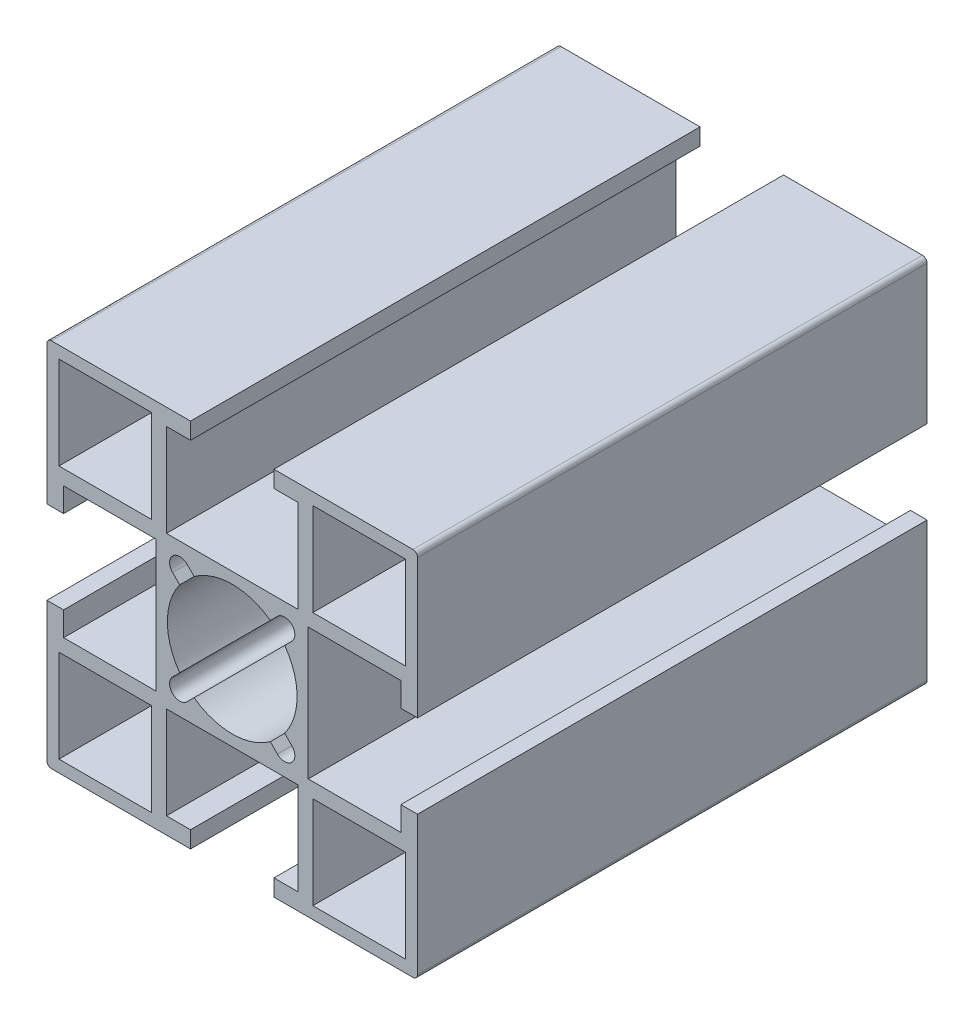
SolidWorks part; units mm, degrees
ref_plane "前视基准面" through (0, 0, 0) normal (0, 0, 1) x (1, 0, 0)
ref_plane "上视基准面" through (0, 0, 0) normal (0, 1, 0) x (1, 0, 0)
ref_plane "右视基准面" through (0, 0, 0) normal (1, 0, 0) x (0, 0, -1)
other "Configuration Table"
sketch "草图1" plane through (0, 0, 0) normal (1, 0, 0) x (0, 0, -1)
  line L0 (0, 0) -> (55, 0)
other "铝型材 40 X 40A X R0.5(1)"
ref_plane "基准面1" through (0, 0, 0) normal (0, 0, -1) x (0, 1, 0)
sketch "Sketch12" plane through (0, 0, 0) normal (0, 0, -1) x (0, 1, 0)
  line L0 (0, 0) -> (0, 16.3773) construction
  line L1 (0, 0) -> (-5.6569, 5.6569) construction
  line L2 (-19.5, 20) -> (-4.5, 20)
  line L3 (-20, 19.5) -> (-20, 4.5)
  line L4 (-19.5, -20) -> (-4.5, -20)
  line L5 (20, 19.5) -> (20, 4.5)
  line L6 (-4.879, 6.4347) -> (-4.1104, 5.6661)
  line L7 (-6.4347, 4.879) -> (-5.6661, 4.1104)
  line L8 (6.4347, 4.879) -> (5.6661, 4.1104)
  line L9 (0, 0) -> (20, 0) construction
  line L10 (4.879, 6.4347) -> (4.1104, 5.6661)
  line L11 (4.879, -6.4347) -> (4.1104, -5.6661)
  line L12 (6.4347, -4.879) -> (5.6661, -4.1104)
  line L13 (-6.4347, -4.879) -> (-5.6661, -4.1104)
  line L14 (-4.879, -6.4347) -> (-4.1104, -5.6661)
  line L15 (-4.5, 20) -> (-4.5, 18.2)
  line L16 (-18.7, 18.7) -> (-8.7, 18.7)
  line L17 (-18.7, 18.7) -> (-18.7, 8.7)
  line L18 (-18.7, 8.7) -> (-8.7, 8.7)
  line L19 (-8.7, 18.7) -> (-8.7, 8.7)
  line L20 (-7.1, 18.2) -> (-4.5, 18.2)
  line L21 (-7.1, 18.2) -> (-7.1, 8.2)
  line L22 (-7.1, 8.2) -> (7.1, 8.2)
  line L23 (7.1, 18.2) -> (7.1, 8.2)
  line L24 (4.5, 20) -> (4.5, 18.2)
  line L25 (4.5, 20) -> (19.5, 20)
  line L26 (4.5, 18.2) -> (7.1, 18.2)
  line L27 (8.7, 18.7) -> (8.7, 8.7)
  line L28 (18.7, 8.7) -> (8.7, 8.7)
  line L29 (18.7, 18.7) -> (18.7, 8.7)
  line L30 (18.7, 18.7) -> (8.7, 18.7)
  line L31 (18.2, 7.1) -> (8.2, 7.1)
  line L32 (18.2, 7.1) -> (18.2, 4.5)
  line L33 (20, 4.5) -> (18.2, 4.5)
  line L34 (8.2, 7.1) -> (8.2, -7.1)
  line L35 (18.2, -7.1) -> (8.2, -7.1)
  line L36 (18.2, -4.5) -> (18.2, -7.1)
  line L37 (20, -4.5) -> (18.2, -4.5)
  line L38 (7.1, -18.2) -> (7.1, -8.2)
  line L39 (7.1, -18.2) -> (4.5, -18.2)
  line L40 (4.5, -20) -> (4.5, -18.2)
  line L41 (7.1, -8.2) -> (-7.1, -8.2)
  line L42 (-7.1, -18.2) -> (-7.1, -8.2)
  line L43 (-4.5, -18.2) -> (-7.1, -18.2)
  line L44 (-4.5, -20) -> (-4.5, -18.2)
  line L45 (-18.2, -7.1) -> (-8.2, -7.1)
  line L46 (-18.2, -7.1) -> (-18.2, -4.5)
  line L47 (-20, -4.5) -> (-18.2, -4.5)
  line L48 (-8.2, -7.1) -> (-8.2, 7.1)
  line L49 (-18.2, 7.1) -> (-8.2, 7.1)
  line L50 (-18.2, 4.5) -> (-18.2, 7.1)
  line L51 (-20, 4.5) -> (-18.2, 4.5)
  line L52 (4.5, -20) -> (19.5, -20)
  line L53 (-20, -4.5) -> (-20, -19.5)
  line L54 (20, -4.5) -> (20, -19.5)
  line L55 (18.7, -18.7) -> (18.7, -8.7)
  line L56 (18.7, -8.7) -> (8.7, -8.7)
  line L57 (8.7, -18.7) -> (8.7, -8.7)
  line L58 (18.7, -18.7) -> (8.7, -18.7)
  line L59 (-8.7, -18.7) -> (-8.7, -8.7)
  line L60 (-18.7, -8.7) -> (-8.7, -8.7)
  line L61 (-18.7, -18.7) -> (-8.7, -18.7)
  line L62 (-18.7, -18.7) -> (-18.7, -8.7)
  arc A0 (-4.1104, 5.6661) -> (4.1104, 5.6661) centre (0, 0) cw
  arc A1 (-4.879, 6.4347) -> (-6.4347, 4.879) centre (-5.6569, 5.6569) ccw
  arc A2 (-4.1104, -5.6661) -> (4.1104, -5.6661) centre (0, 0) ccw
  arc A3 (-5.6661, 4.1104) -> (-5.6661, -4.1104) centre (0, 0) ccw
  arc A4 (6.4347, 4.879) -> (4.879, 6.4347) centre (5.6569, 5.6569) ccw
  arc A5 (4.879, -6.4347) -> (6.4347, -4.879) centre (5.6569, -5.6569) ccw
  arc A6 (-6.4347, -4.879) -> (-4.879, -6.4347) centre (-5.6569, -5.6569) ccw
  arc A7 (5.6661, 4.1104) -> (5.6661, -4.1104) centre (0, 0) cw
  arc A8 (-19.5, 20) -> (-20, 19.5) centre (-19.5, 19.5) ccw
  arc A9 (19.5, 20) -> (20, 19.5) centre (19.5, 19.5) cw
  arc A10 (19.5, -20) -> (20, -19.5) centre (19.5, -19.5) ccw
  arc A11 (-20, -19.5) -> (-19.5, -20) centre (-19.5, -19.5) ccw
  point P86 (20, 20)
  point P87 (-20, 20)
  point P88 (-20, -20)
  point P89 (20, -20)
  point P90 (0, 0)
  dimension "D2" = 7
  dimension "D3" = 45
  dimension "D4" = 1.1
  dimension "D5" = 1.8
  dimension "D6" = 8
  dimension "D7" = 1.3
  dimension "D8" = 14.2
  dimension "D10" = 10
  dimension "D11" = 10
  dimension "D12" = 40
  dimension "D13" = 9
  dimension "D14" = 0.5
  dimension "D9" = 1.3
